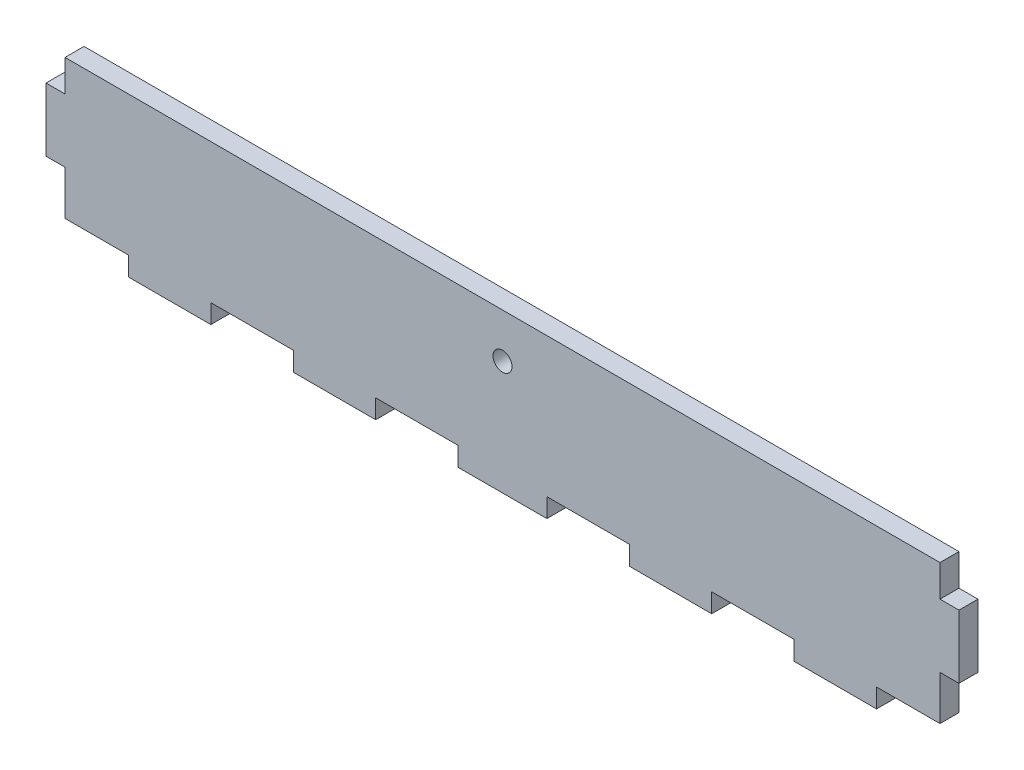
SolidWorks part; units mm, degrees
ref_plane "Front Plane" through (0, 0, 0) normal (0, 0, 1) x (1, 0, 0)
ref_plane "Top Plane" through (0, 0, 0) normal (0, 1, 0) x (1, 0, 0)
ref_plane "Right Plane" through (0, 0, 0) normal (1, 0, 0) x (0, 0, -1)
sketch "Sketch1" plane through (0, 0, 0) normal (0, 0, 1) x (1, 0, 0)
  line L0 (0, 17) -> (0, 22)
  line L1 (0, 0) -> (10, 0)
  line L2 (0, 0) -> (0, 7)
  line L3 (0, 22) -> (138, 22)
  line L4 (138, 0) -> (138, 7)
  line L5 (0, 17) -> (-3, 17)
  line L6 (138, 17) -> (138, 22)
  line L7 (0, 7) -> (-3, 7)
  line L8 (-3, 17) -> (-3, 7)
  line L9 (138, 17) -> (141, 17)
  line L10 (23, 0) -> (36, 0)
  line L11 (138, 7) -> (141, 7)
  line L12 (141, 17) -> (141, 7)
  line L14 (10, 0) -> (10, -3)
  line L15 (10, -3) -> (23, -3)
  line L16 (23, 0) -> (23, -3)
  line L18 (36, 0) -> (36, -3)
  line L19 (36, -3) -> (49, -3)
  line L20 (49, 0) -> (49, -3)
  line L22 (62, 0) -> (62, -3)
  line L23 (62, -3) -> (76, -3)
  line L24 (76, 0) -> (76, -3)
  line L26 (89, 0) -> (89, -3)
  line L27 (89, -3) -> (102, -3)
  line L28 (102, 0) -> (102, -3)
  line L30 (115, 0) -> (115, -3)
  line L31 (115, -3) -> (128, -3)
  line L32 (128, 0) -> (128, -3)
  line L33 (49, 0) -> (62, 0)
  line L34 (76, 0) -> (89, 0)
  line L35 (102, 0) -> (115, 0)
  line L36 (128, 0) -> (138, 0)
  circle A1 centre (69, 15) radius 1.5
  dimension "D17" = 72
  dimension "D18" = 3
  dimension "D1" = 138
  dimension "D2" = 22
  dimension "D3" = 5
  dimension "D4" = 7
  dimension "D5" = 3
  dimension "D6" = 14
  dimension "D7" = 10
  dimension "D8" = 10
  dimension "D9" = 13
  dimension "D10" = 13
  dimension "D11" = 13
  dimension "D12" = 13
  dimension "D13" = 13
  dimension "D14" = 13
  dimension "D15" = 13
  dimension "D16" = 3
  dimension "D23" = 7
extrude "Boss-Extrude1" add sketch "Sketch1" along normal blind 3
